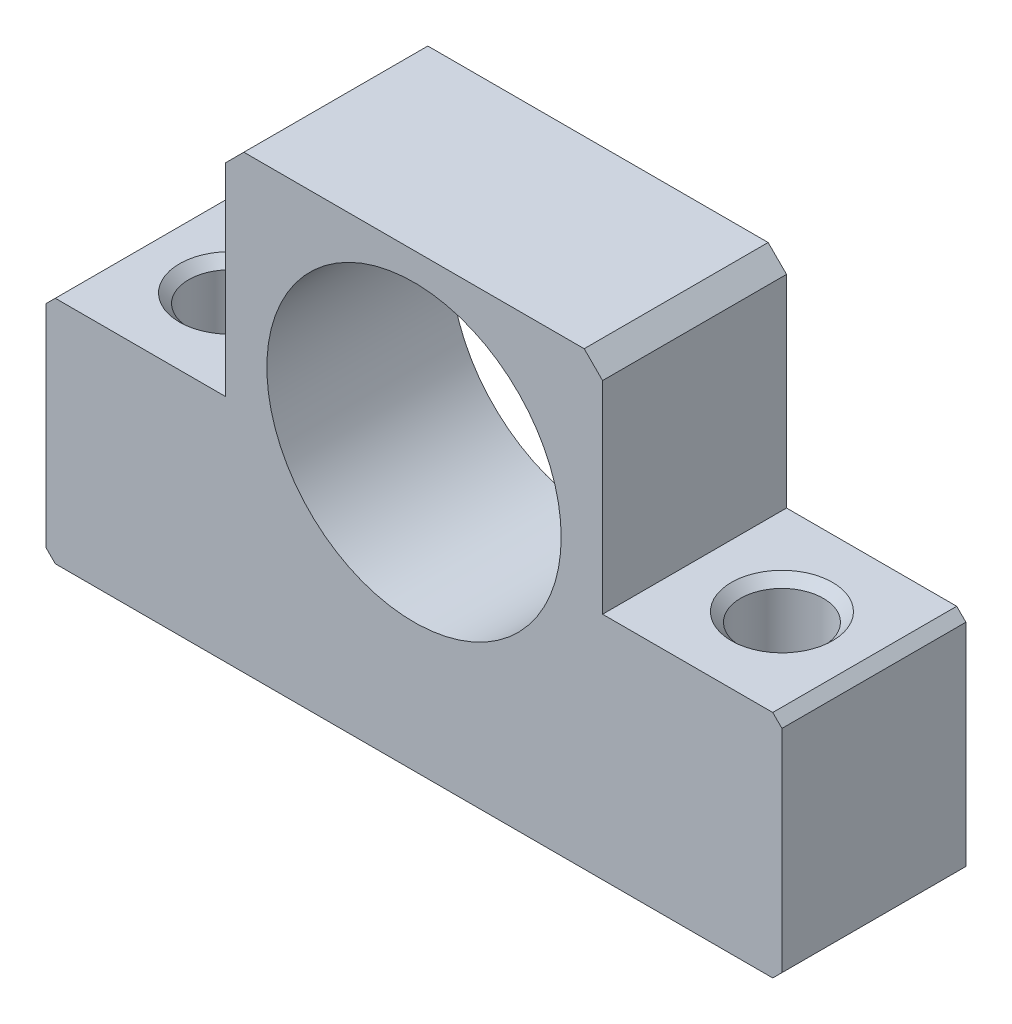
SolidWorks part; units mm, degrees
ref_plane "Front Plane" through (0, 0, 0) normal (0, 0, 1) x (1, 0, 0)
ref_plane "Top Plane" through (0, 0, 0) normal (0, 1, 0) x (1, 0, 0)
ref_plane "Right Plane" through (0, 0, 0) normal (1, 0, 0) x (0, 0, -1)
ref_plane "Plane1" through (0, 0, 0) normal (0, 0, 1) x (1, 0, 0)
sketch "Sketch1" plane through (0, 0, 0) normal (0, 0, 1) x (1, 0, 0)
  line L0 (-40, -29) -> (-39, -30)
  line L1 (-39, -30) -> (39, -30)
  line L2 (39, -30) -> (40, -29)
  line L3 (40, -29) -> (40, -6)
  line L4 (40, -6) -> (39, -5)
  line L5 (39, -5) -> (20.5, -5)
  line L6 (20.5, -5) -> (20.5, 17)
  line L7 (20.5, 17) -> (18.5, 19)
  line L8 (18.5, 19) -> (-18.5, 19)
  line L9 (-18.5, 19) -> (-20.5, 17)
  line L10 (-20.5, 17) -> (-20.5, -5)
  line L11 (-20.5, -5) -> (-39, -5)
  line L12 (-39, -5) -> (-40, -6)
  line L13 (-40, -6) -> (-40, -29)
  circle A0 centre (0, 0) radius 16
extrude "Boss-Extrude1" add sketch "Sketch1" against normal blind 20
ref_plane "Plane2" through (0, 0, -10) normal (0, 0, 1) x (1, 0, 0)
sketch "Sketch2" plane through (0, 0, -10) normal (0, 0, 1) x (1, 0, 0)
  line L0 (30, -5) -> (35.5, -5)
  line L1 (35.5, -5) -> (34.5, -6)
  line L2 (34.5, -6) -> (34.5, -29)
  line L3 (34.5, -29) -> (35.5, -30)
  line L4 (35.5, -30) -> (30, -30)
  line L5 (30, -30) -> (30, -5)
  line L6 (30, -30) -> (30, -5) construction
revolve "Cut-Revolve1" cut sketch "Sketch2" angle 360 about L6
ref_plane "Plane3" through (0, 0, -10) normal (0, 0, 1) x (1, 0, 0)
sketch "Sketch3" plane through (0, 0, -10) normal (0, 0, 1) x (1, 0, 0)
  line L0 (-30, -5) -> (-24.5, -5)
  line L1 (-24.5, -5) -> (-25.5, -6)
  line L2 (-25.5, -6) -> (-25.5, -29)
  line L3 (-25.5, -29) -> (-24.5, -30)
  line L4 (-24.5, -30) -> (-30, -30)
  line L5 (-30, -30) -> (-30, -5)
  line L6 (-30, -30) -> (-30, -5) construction
revolve "Cut-Revolve2" cut sketch "Sketch3" angle 360 about L6
